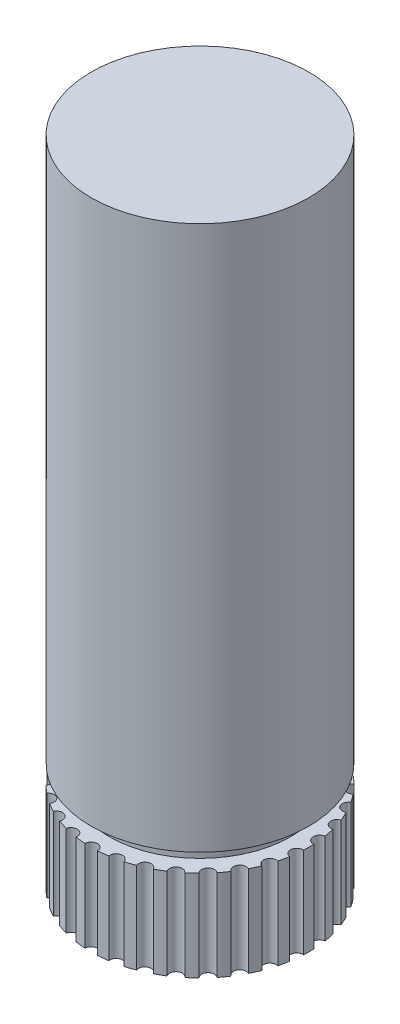
SolidWorks part; units mm, degrees
ref_plane "Alzado" through (0, 0, 0) normal (0, 0, 1) x (1, 0, 0)
ref_plane "Planta" through (0, 0, 0) normal (0, 1, 0) x (1, 0, 0)
ref_plane "Vista lateral" through (0, 0, 0) normal (1, 0, 0) x (0, 0, -1)
sketch "Croquis1" plane through (0, 0, 0) normal (0, 1, 0) x (1, 0, 0)
  circle A0 centre (0, 0) radius 6
  dimension "D1" = 12
extrude "Saliente-Extruir1" add sketch "Croquis1" along normal blind 30
sketch "Croquis3" plane through (0, 0, 0) normal (0, -1, 0) x (1, 0, 0)
  circle A0 centre (0, 0) radius 5
  dimension "D1" = 10
extrude "Saliente-Extruir2" add sketch "Croquis3" along normal blind 1
sketch "Croquis4" plane through (0, -1, 0) normal (0, -1, 0) x (1, 0, 0)
  circle A0 centre (0, 0) radius 6
extrude "Saliente-Extruir3" add sketch "Croquis4" along normal blind 5
sketch "Croquis5" plane through (0, -6, 0) normal (0, -1, 0) x (1, 0, 0)
  line L0 (0, 6) -> (0, 0) construction
  circle A0 centre (0, 6) radius 0.35
  circle A1 centre (0, 0) radius 6 construction
  circle A2 centre (1.2475, 5.8689) radius 0.35
  circle A3 centre (2.4404, 5.4813) radius 0.35
  circle A4 centre (3.5267, 4.8541) radius 0.35
  circle A5 centre (4.4589, 4.0148) radius 0.35
  circle A6 centre (5.1962, 3) radius 0.35
  circle A7 centre (5.7063, 1.8541) radius 0.35
  circle A8 centre (5.9671, 0.6272) radius 0.35
  circle A9 centre (5.9671, -0.6272) radius 0.35
  circle A10 centre (5.7063, -1.8541) radius 0.35
  circle A11 centre (5.1962, -3) radius 0.35
  circle A12 centre (4.4589, -4.0148) radius 0.35
  circle A13 centre (3.5267, -4.8541) radius 0.35
  circle A14 centre (2.4404, -5.4813) radius 0.35
  circle A15 centre (1.2475, -5.8689) radius 0.35
  circle A16 centre (0, -6) radius 0.35
  circle A17 centre (-1.2475, -5.8689) radius 0.35
  circle A18 centre (-2.4404, -5.4813) radius 0.35
  circle A19 centre (-3.5267, -4.8541) radius 0.35
  circle A20 centre (-4.4589, -4.0148) radius 0.35
  circle A21 centre (-5.1962, -3) radius 0.35
  circle A22 centre (-5.7063, -1.8541) radius 0.35
  circle A23 centre (-5.9671, -0.6272) radius 0.35
  circle A24 centre (-5.9671, 0.6272) radius 0.35
  circle A25 centre (-5.7063, 1.8541) radius 0.35
  circle A26 centre (-5.1962, 3) radius 0.35
  circle A27 centre (-4.4589, 4.0148) radius 0.35
  circle A28 centre (-3.5267, 4.8541) radius 0.35
  circle A29 centre (-2.4404, 5.4813) radius 0.35
  circle A30 centre (-1.2475, 5.8689) radius 0.35
  point P66 (0, 0)
  dimension "D1" = 0.7
  dimension "D2" = 30
extrude "Cortar-Extruir1" cut sketch "Croquis5" against normal blind 5
